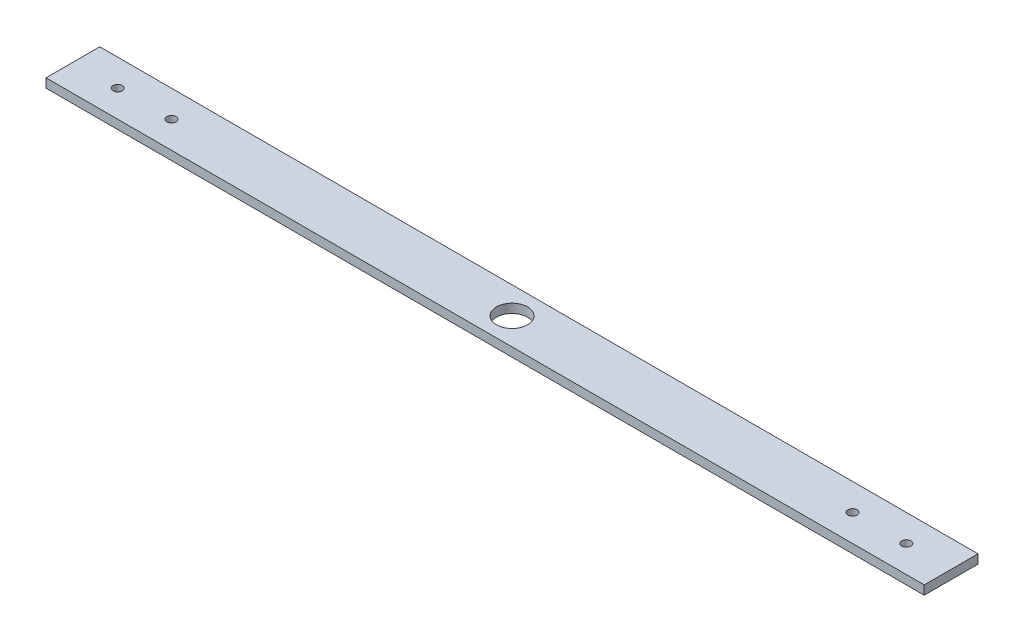
SolidWorks part; units mm, degrees
material "6061-T6 (SS)"
ref_plane "Front Plane" through (0, 0, 0) normal (0, 0, 1) x (1, 0, 0)
ref_plane "Top Plane" through (0, 0, 0) normal (0, 1, 0) x (1, 0, 0)
ref_plane "Right Plane" through (0, 0, 0) normal (1, 0, 0) x (0, 0, -1)
sketch "Sketch1" plane through (0, 0, 0) normal (0, 1, 0) x (1, 0, 0)
  line L1 (-311.15, 19.05) -> (311.15, 19.05)
  line L2 (-311.15, 19.05) -> (-311.15, -19.05)
  line L3 (-311.15, -19.05) -> (311.15, -19.05)
  line L4 (311.15, 19.05) -> (311.15, -19.05)
  line L5 (-311.15, 19.05) -> (311.15, -19.05) construction
  line L6 (-311.15, -19.05) -> (311.15, 19.05) construction
  point P0 (0, 0)
  dimension "D1" = 38.1
  dimension "D2" = 622.3
extrude "Boss-Extrude1" add sketch "Sketch1" along normal blind 6.35
sketch "Sketch2" plane through (0, 6.35, 0) normal (0, 1, 0) x (1, 0, 0)
  circle A0 centre (0, 0) radius 11
  dimension "D1" = 22
extrude "Cut-Extrude1" cut sketch "Sketch2" against normal blind 7.62 and the other way through all
hole_wizard "F (0.257) Diameter Hole2" positions "Sketch3" profile "Sketch4" hole size "F" standard "ANSI Inch" end condition through all
sketch "Sketch3" plane through (0, 6.35, 0) normal (0, 1, 0) x (1, 0, 0)
  line L0 (0, 0) -> (-311.15, 0) construction
  line L1 (-311.15, 19.05) -> (-311.15, -19.05) construction
  point P8 (-241.3, 0)
  point P10 (-279.4, 0)
  dimension "D1" = 31.75
  dimension "D2" = 69.85
sketch "Sketch4" plane through (-279.4, 6.35, 0) normal (1, 0, 0) x (0, 0, 1)
  line L0 (0, 0) -> (0, 6.35)
  line L1 (0, 6.35) -> (3.2639, 6.35)
  line L2 (3.2639, 6.35) -> (3.2639, 0)
  line L5 (3.2639, 0) -> (0, 0)
  line L11 (0, -6.35) -> (0, 107.95) construction
  dimension "Thru Hole Dia." = 6.5278
  dimension "Thru Hole Depth" = 6.35
mirror "Mirror1" about plane through (0, 0, 0) normal (1, 0, 0) of "F (0.257) Diameter Hole2"
